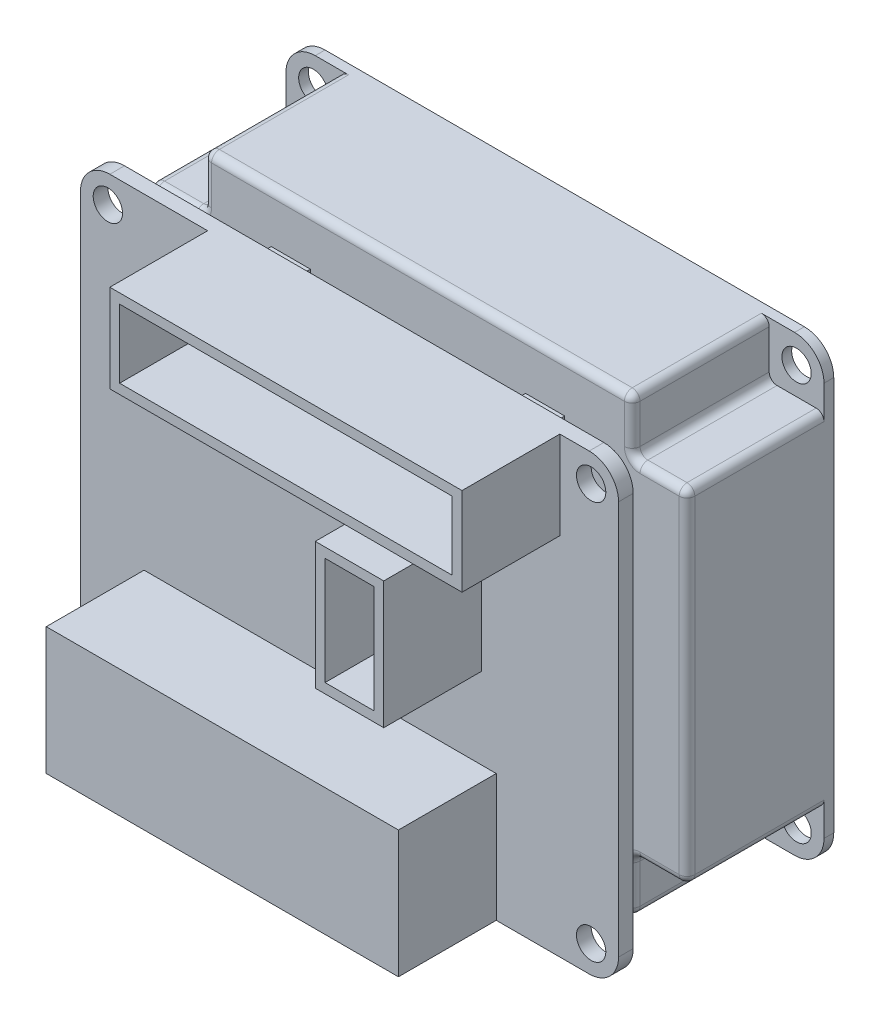
SolidWorks part; units mm, degrees
ref_plane "前视基准面" through (0, 0, 0) normal (0, 0, 1) x (1, 0, 0)
ref_plane "上视基准面" through (0, 0, 0) normal (0, 1, 0) x (1, 0, 0)
ref_plane "右视基准面" through (0, 0, 0) normal (1, 0, 0) x (0, 0, -1)
sketch "草图1" plane through (0, 0, 0) normal (0, 0, 1) x (1, 0, 0)
  line L1 (-27.5, 23.15) -> (27.5, 23.15)
  line L2 (-27.5, 23.15) -> (-27.5, -23.15)
  line L3 (-27.5, -23.15) -> (27.5, -23.15)
  line L4 (27.5, 23.15) -> (27.5, -23.15)
  line L5 (-27.5, 23.15) -> (27.5, -23.15) construction
  line L6 (-27.5, -23.15) -> (27.5, 23.15) construction
  point P0 (0, 0)
  dimension "D1" = 55
  dimension "D2" = 46.3
extrude "凸台-拉伸1" add sketch "草图1" along normal blind 15
sketch "草图2" plane through (0, 0, 15) normal (0, 0, 1) x (1, 0, 0)
  line L1 (-27.5, 23.15) -> (-21.9, 23.15)
  line L2 (-27.5, 23.15) -> (-27.5, 17.55)
  line L3 (-27.5, 17.55) -> (-21.9, 17.55)
  line L4 (-21.9, 23.15) -> (-21.9, 17.55)
  dimension "D1" = 5.6
extrude "切除-拉伸1" cut sketch "草图2" against normal blind 14
sketch "草图3" plane through (0, 0, 1) normal (0, 0, 1) x (1, 0, 0)
  circle A0 centre (-24.7, 20.35) radius 1.5
  dimension "D1" = 3
extrude "切除-拉伸2" cut sketch "草图3" against normal up to next (1 mm away)
mirror "镜向1" about plane through (0, 0, 0) normal (0, 1, 0) of "切除-拉伸2", "切除-拉伸1"
mirror "镜向2" about plane through (0, 0, 0) normal (1, 0, 0) of "镜向1", "切除-拉伸1", "切除-拉伸2"
fillet "圆角1" radius 3 4 edges at (-27.5, -23.15, 0.5) (27.5, -23.15, 0.5) (27.5, 23.15, 0.5) (-27.5, 23.15, 0.5)
fillet "圆角2" radius 0.8 24 edges at (24.7, -17.55, 15) (-21.9, -20.35, 15) (21.9, 17.55, 8) (-21.9, 17.55, 8) (27.5, -17.55, 8) (21.9, -20.35, 15) (21.9, -17.55, 8) (21.9, -23.15, 8) (-27.5, 0, 15) (-27.5, 17.55, 8) (-24.7, 17.55, 15) (-21.9, 20.35, 15) (-21.9, 23.15, 8) (0, 23.15, 15) (21.9, 23.15, 8) (21.9, 20.35, 15) (24.7, 17.55, 15) (27.5, 17.55, 8) (27.5, 0, 15) (0, -23.15, 15) (-24.7, -17.55, 15) (-21.9, -17.55, 8) (-21.9, -23.15, 8) (-27.5, -17.55, 8)
sketch "草图5" plane through (0, 0, 15) normal (0, 0, 1) x (1, 0, 0)
  line L0 (0, 18) -> (0, -18.928) construction
  line L1 (-15, 18) -> (-11, 18)
  line L2 (-15, 18) -> (-15, -18)
  line L3 (-15, -18) -> (-11, -18)
  line L4 (-11, 18) -> (-11, -18)
  line L5 (-15, 18) -> (-11, -18) construction
  line L6 (-15, -18) -> (-11, 18) construction
  line L7 (15, -18) -> (11, -18)
  line L8 (15, 18) -> (15, -18)
  line L9 (11, 18) -> (11, -18)
  line L10 (15, 18) -> (11, 18)
  point P0 (-13, 0)
  dimension "D1" = 4
  dimension "D2" = 36
  dimension "D3" = 11
extrude "凸台-拉伸2" add sketch "草图5" along normal blind 5.5
sketch "草图6" plane through (0, 0, 20.5) normal (0, 0, 1) x (1, 0, 0)
  line L0 (-27.5, -20.15) -> (-27.5, -16.75) construction
  line L1 (24.5, 23.15) -> (-24.5, 23.15)
  line L2 (27.5, 20.15) -> (27.5, -20.15)
  line L3 (24.5, -23.15) -> (-24.5, -23.15)
  line L4 (-27.5, 20.15) -> (-27.5, -20.15)
  line L5 (27.5, 23.15) -> (-27.5, -23.15) construction
  line L6 (27.5, -23.15) -> (-27.5, 23.15) construction
  line L9 (-21.1, -23.15) -> (-24.5, -23.15) construction
  circle A0 centre (-24.7, 20.35) radius 1.5
  circle A1 centre (24.7, 20.35) radius 1.5
  circle A2 centre (-24.7, -20.35) radius 1.5
  circle A3 centre (24.7, -20.35) radius 1.5
  arc A4 (-24.5, -23.15) -> (-27.5, -20.15) centre (-24.5, -20.15) cw
  arc A5 (27.5, -20.15) -> (24.5, -23.15) centre (24.5, -20.15) cw
  arc A6 (24.5, 23.15) -> (27.5, 20.15) centre (24.5, 20.15) cw
  arc A7 (-24.5, 23.15) -> (-27.5, 20.15) centre (-24.5, 20.15) ccw
  point P0 (0, 0)
  dimension "D1" = 3
extrude "凸台-拉伸3" add sketch "草图6" along normal blind 1.5
sketch "草图7" plane through (0, 0, 22) normal (0, 0, 1) x (1, 0, 0)
  line L0 (-27.5, 20.15) -> (-27.5, -20.15) construction
  line L1 (-14.5, 23.15) -> (21.5, 23.15)
  line L2 (-14.5, 23.15) -> (-14.5, 14.15)
  line L3 (-14.5, 14.15) -> (21.5, 14.15)
  line L4 (21.5, 23.15) -> (21.5, 14.15)
  line L5 (-14.5, 23.15) -> (21.5, 14.15) construction
  line L6 (-14.5, 14.15) -> (21.5, 23.15) construction
  line L7 (24.5, 23.15) -> (-24.5, 23.15) construction
  line L8 (-13.5, 15.15) -> (20.5, 15.15)
  line L9 (20.5, 22.15) -> (20.5, 15.15)
  line L10 (-13.5, 22.15) -> (20.5, 22.15)
  line L11 (-13.5, 22.15) -> (-13.5, 15.15)
  line L12 (27.5, -20.15) -> (27.5, 20.15) construction
  line L13 (6.5, 11.15) -> (13.5, 11.15)
  line L14 (6.5, 11.15) -> (6.5, -1.85)
  line L15 (6.5, -1.85) -> (13.5, -1.85)
  line L16 (13.5, 11.15) -> (13.5, -1.85)
  line L17 (6.5, 11.15) -> (13.5, -1.85) construction
  line L18 (6.5, -1.85) -> (13.5, 11.15) construction
  line L19 (-24.5, -23.15) -> (24.5, -23.15) construction
  line L20 (-21, -10.15) -> (15, -10.15)
  line L21 (-21, -10.15) -> (-21, -23.15)
  line L22 (-21, -23.15) -> (15, -23.15)
  line L23 (15, -10.15) -> (15, -23.15)
  line L24 (-21, -10.15) -> (15, -23.15) construction
  line L25 (-21, -23.15) -> (15, -10.15) construction
  line L26 (7.5, 10.15) -> (7.5, -0.85)
  line L27 (7.5, -0.85) -> (12.5, -0.85)
  line L28 (12.5, 10.15) -> (12.5, -0.85)
  line L29 (7.5, 10.15) -> (12.5, 10.15)
  point P0 (3.5, 18.65)
  point P13 (10, 4.65)
  point P20 (-3, -16.65)
  dimension "D1" = 13
  dimension "D2" = 36
  dimension "D3" = 9
  dimension "D5" = 7
  dimension "D6" = 13
  dimension "D7" = 14
  dimension "D8" = 25
  dimension "D9" = 12.5
  dimension "D10" = 36
  dimension "D11" = 13
  dimension "D4" = 1
  dimension "D12" = 1
extrude "凸台-拉伸4" add sketch "草图7" along normal blind 10
sketch "草图9" plane through (0, -23.15, 0) normal (0, -1, 0) x (1, 0, 0)
  line L0 (-21, 32) -> (15, 32) construction
  line L1 (-20, 31) -> (14, 31)
  line L2 (-20, 31) -> (-20, 23)
  line L3 (-20, 23) -> (14, 23)
  line L4 (14, 31) -> (14, 23)
  line L5 (-20, 31) -> (14, 23) construction
  line L6 (-20, 23) -> (14, 31) construction
  line L7 (-21, 32) -> (-21, 22) construction
  line L8 (15, 32) -> (15, 22) construction
  line L9 (-24.5, 22) -> (-21, 22) construction
  point P0 (-3, 27)
  dimension "D1" = 1
  dimension "D2" = 1
  dimension "D3" = 1
  dimension "D4" = 1
extrude "切除-拉伸3" cut sketch "草图9" against normal blind 11
